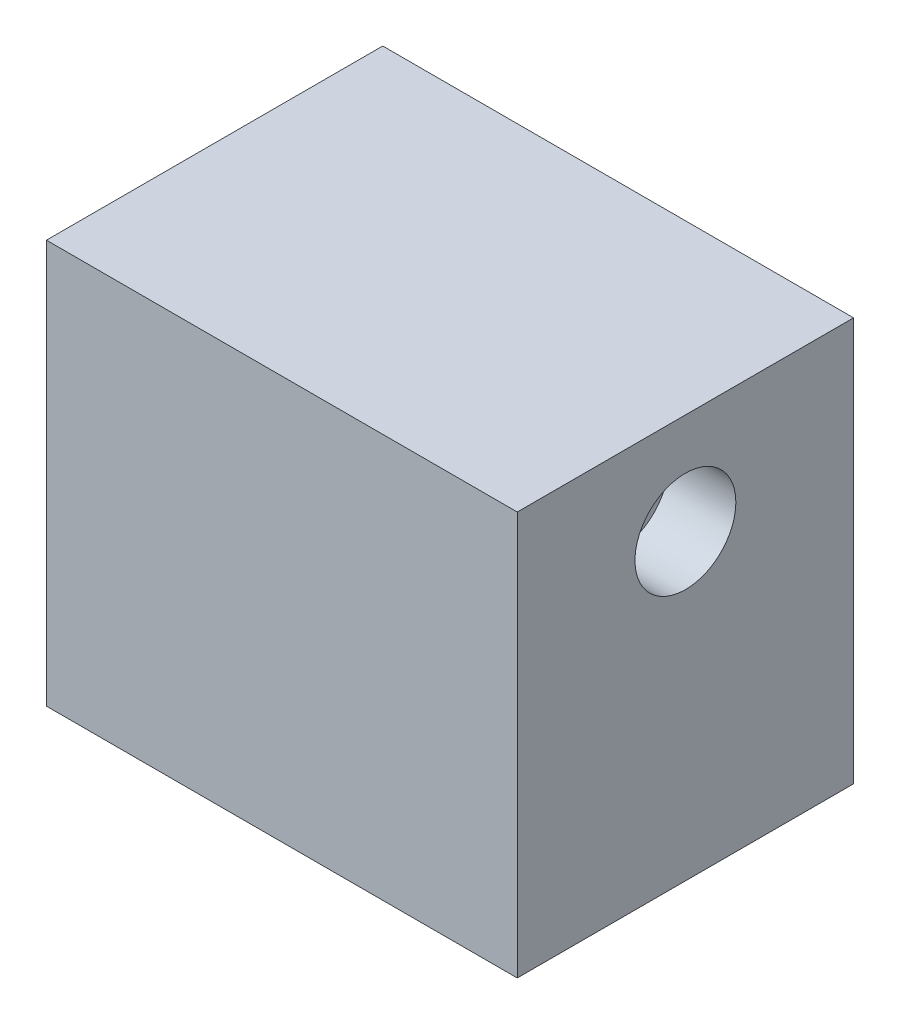
SolidWorks part; units mm, degrees
ref_plane "前视基准面" through (0, 0, 0) normal (0, 0, 1) x (1, 0, 0)
ref_plane "上视基准面" through (0, 0, 0) normal (0, 1, 0) x (1, 0, 0)
ref_plane "右视基准面" through (0, 0, 0) normal (1, 0, 0) x (0, 0, -1)
sketch "Sketch1" plane through (0, 0, 0) normal (0, 1, 0) x (1, 0, 0)
  line L1 (0, 0) -> (35, 0)
  line L2 (0, 0) -> (0, 25)
  line L3 (0, 25) -> (35, 25)
  line L4 (35, 0) -> (35, 25)
  dimension "D1" = 35
  dimension "D2" = 25
extrude "Boss-Extrude1" add sketch "Sketch1" along normal blind 30
sketch "Sketch2" plane through (35, 0, 0) normal (1, 0, 0) x (0, 0, -1)
  line L0 (0, 30) -> (0, 0) construction
  line L1 (0, 30) -> (25, 30) construction
  circle A0 centre (12.5, 22.5) radius 3.75
  point P4 (0, 0)
  point P6 (13.0578, 24.0378)
  dimension "D1" = 7.5
  dimension "D2" = 12.5
  dimension "D3" = 7.5
extrude "Cut-Extrude1" cut sketch "Sketch2" against normal blind 5
sketch "Sketch3" plane through (0, 0, 0) normal (-1, 0, 0) x (0, 0, 1)
  line L0 (-25, 30) -> (0, 30) construction
  line L1 (0, 30) -> (0, 0) construction
  circle A0 centre (-12.5, 22.5) radius 3.75
  dimension "D1" = 7.5
  dimension "D2" = 7.5
  dimension "D3" = 12.5
extrude "Cut-Extrude2" cut sketch "Sketch3" against normal blind 5
